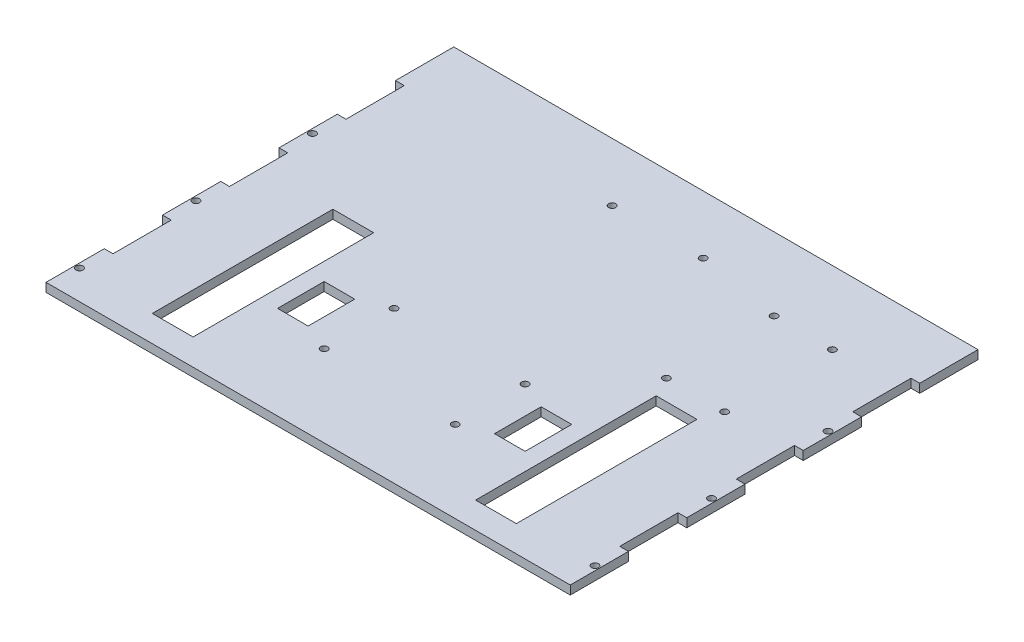
SolidWorks part; units mm, degrees
material "Acrylic (Medium-high impact)"
ref_plane "Front" through (0, 0, 0) normal (0, 0, 1) x (1, 0, 0)
ref_plane "Top" through (0, 0, 0) normal (0, 1, 0) x (1, 0, 0)
ref_plane "Right" through (0, 0, 0) normal (1, 0, 0) x (0, 0, -1)
sketch "Sketch1" plane through (0, 0, 0) normal (0, 1, 0) x (1, 0, 0)
  line L0 (-110.49, 0) -> (110.49, 0) construction
  line L5 (-114.3, -88.9) -> (114.3, -88.9)
  line L7 (-114.3, 88.9) -> (114.3, 88.9)
  line L9 (0, 88.9) -> (0, -88.9) construction
  line L10 (-28.575, -22.86) -> (-28.575, -53.34) construction
  line L11 (-40.64, -27.94) -> (-53.975, -27.94)
  line L12 (-40.64, -27.94) -> (-40.64, -48.26)
  line L13 (-40.64, -48.26) -> (-53.975, -48.26)
  line L14 (-53.975, -27.94) -> (-53.975, -48.26)
  line L15 (-114.3, -38.1) -> (114.3, -38.1) construction
  line L16 (61.595, 1.27) -> (61.595, -77.47)
  line L17 (-79.375, 1.27) -> (-61.595, 1.27)
  line L18 (-79.375, 1.27) -> (-79.375, -77.47)
  line L19 (-79.375, -77.47) -> (-61.595, -77.47)
  line L20 (-61.595, 1.27) -> (-61.595, -77.47)
  line L21 (79.375, -77.47) -> (61.595, -77.47)
  line L22 (79.375, 1.27) -> (79.375, -77.47)
  line L23 (79.375, 1.27) -> (61.595, 1.27)
  line L24 (53.975, -27.94) -> (53.975, -48.26)
  line L25 (40.64, -48.26) -> (53.975, -48.26)
  line L26 (40.64, -27.94) -> (40.64, -48.26)
  line L27 (40.64, -27.94) -> (53.975, -27.94)
  line L28 (114.3, 63.5) -> (110.49, 63.5)
  line L29 (110.49, 63.5) -> (110.49, 38.1)
  line L30 (110.49, 38.1) -> (114.3, 38.1)
  line L31 (114.3, 63.5) -> (114.3, 88.9)
  line L32 (114.3, 12.7) -> (114.3, 38.1)
  line L33 (114.3, 12.7) -> (110.49, 12.7)
  line L34 (110.49, 12.7) -> (110.49, -12.7)
  line L35 (110.49, -12.7) -> (114.3, -12.7)
  line L36 (114.3, -38.1) -> (114.3, -12.7)
  line L37 (114.3, -38.1) -> (110.49, -38.1)
  line L38 (110.49, -38.1) -> (110.49, -63.5)
  line L39 (110.49, -63.5) -> (114.3, -63.5)
  line L40 (114.3, -63.5) -> (114.3, -88.9)
  line L41 (-114.3, 63.5) -> (-114.3, 88.9)
  line L42 (-114.3, -63.5) -> (-114.3, -88.9)
  line L43 (-110.49, -63.5) -> (-114.3, -63.5)
  line L44 (-110.49, -38.1) -> (-110.49, -63.5)
  line L45 (-114.3, -38.1) -> (-110.49, -38.1)
  line L46 (-114.3, -38.1) -> (-114.3, -12.7)
  line L47 (-110.49, -12.7) -> (-114.3, -12.7)
  line L48 (-110.49, 12.7) -> (-110.49, -12.7)
  line L49 (-114.3, 12.7) -> (-110.49, 12.7)
  line L50 (-114.3, 12.7) -> (-114.3, 38.1)
  line L51 (-110.49, 38.1) -> (-114.3, 38.1)
  line L52 (-110.49, 63.5) -> (-110.49, 38.1)
  line L53 (-114.3, 63.5) -> (-110.49, 63.5)
  line L54 (114.3, -76.2) -> (-114.3, -76.2) construction
  line L55 (112.395, -63.5) -> (112.395, -88.9) construction
  line L56 (112.395, -76.2) -> (-112.395, -76.2) construction
  line L57 (112.395, -76.2) -> (112.395, -25.4) construction
  circle A0 centre (-28.575, -22.86) radius 1.524
  circle A1 centre (-28.575, -53.34) radius 1.524
  circle A2 centre (28.575, -53.34) radius 1.524
  circle A3 centre (28.575, -22.86) radius 1.524
  circle A4 centre (57.15, 57.15) radius 1.524
  circle A5 centre (57.15, 10.16) radius 1.524
  circle A6 centre (82.55, 10.16) radius 1.524
  circle A7 centre (82.55, 57.15) radius 1.524
  circle A11 centre (112.395, -76.2) radius 1.524
  circle A16 centre (-112.395, -76.2) radius 1.524
  circle A17 centre (-112.395, -25.4) radius 1.524
  circle A18 centre (-112.395, 25.4) radius 1.524
  circle A19 centre (112.395, -25.4) radius 1.524
  circle A20 centre (112.395, 25.4) radius 1.524
  circle A21 centre (-19.8501, 63.5) radius 1.524
  circle A22 centre (19.8501, 63.5) radius 1.524
  point P0 (0, 0)
  point P11 (0, 0)
  point P17 (-61.595, -38.1)
  point P18 (-28.575, -38.1)
  point P20 (-40.64, -38.1)
  point P73 (-110.49, 0)
  dimension "D4" = 3.048
  dimension "D13" = 3.048
  dimension "D22" = 3.048
  dimension "D1" = 228.6
  dimension "D2" = 177.8
  dimension "D3" = 30.48
  dimension "D5" = 20.32
  dimension "D6" = 13.335
  dimension "D7" = 78.74
  dimension "D8" = 17.78
  dimension "D9" = 25.4
  dimension "D10" = 50.8
  dimension "D11" = 50.8
  dimension "D12" = 57.15
  dimension "D14" = 46.99
  dimension "D15" = 25.4
  dimension "D16" = 3
  dimension "D17" = 31.75
  dimension "D18" = 25.4
  dimension "D19" = 3.81
  dimension "D20" = 25.4
  dimension "D21" = 171.45
  dimension "D23" = 2
  dimension "D25" = 1.905
  dimension "D26" = 50.8
  dimension "D27" = 90
  dimension "D28" = 39.7002
  dimension "D29" = 25.4
  dimension "D24" = 3
extrude "Boss-Extrude1" add sketch "Sketch1" along normal blind 3.81
